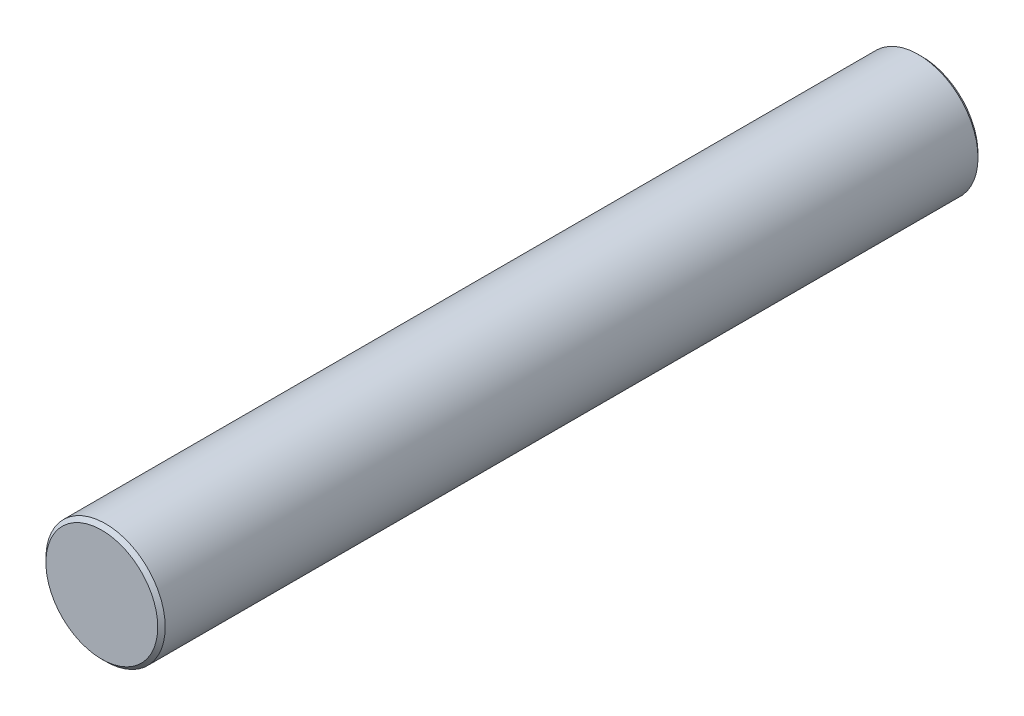
SolidWorks part; units mm, degrees
material "1.0035 (S185)"
ref_plane "Płaszczyzna przednia" through (0, 0, 0) normal (0, 0, 1) x (1, 0, 0)
ref_plane "Płaszczyzna górna" through (0, 0, 0) normal (0, 1, 0) x (1, 0, 0)
ref_plane "Płaszczyzna prawa" through (0, 0, 0) normal (1, 0, 0) x (0, 0, -1)
sketch "Szkic1" plane through (0, 0, 0) normal (0, 0, 1) x (1, 0, 0)
  circle A0 centre (-33.6106, 0) radius 8 construction
  circle A1 centre (-33.6106, 0) radius 8
extrude "Dodanie-wyciągnięcie1" add sketch "Szkic1" along normal mid plane 110
chamfer "Sfazowanie1" distance 0.5 angle 45 2 edges at (-25.6106, 0, -55) (-25.6106, 0, 55)
ref_plane "Płaszczyzna1" through (-41.6106, 0, 0) normal (-1, 0, 0) x (0, 0, 1)
sketch "Szkic2" plane through (-41.6106, 0, 0) normal (-1, 0, 0) x (0, 0, 1)
  circle A0 centre (50.35, 0) radius 3
  dimension "D1" = 6
extrude "Wytnij-wyciągnięcie1" cut sketch "Szkic2" against normal blind 10 draft 5
